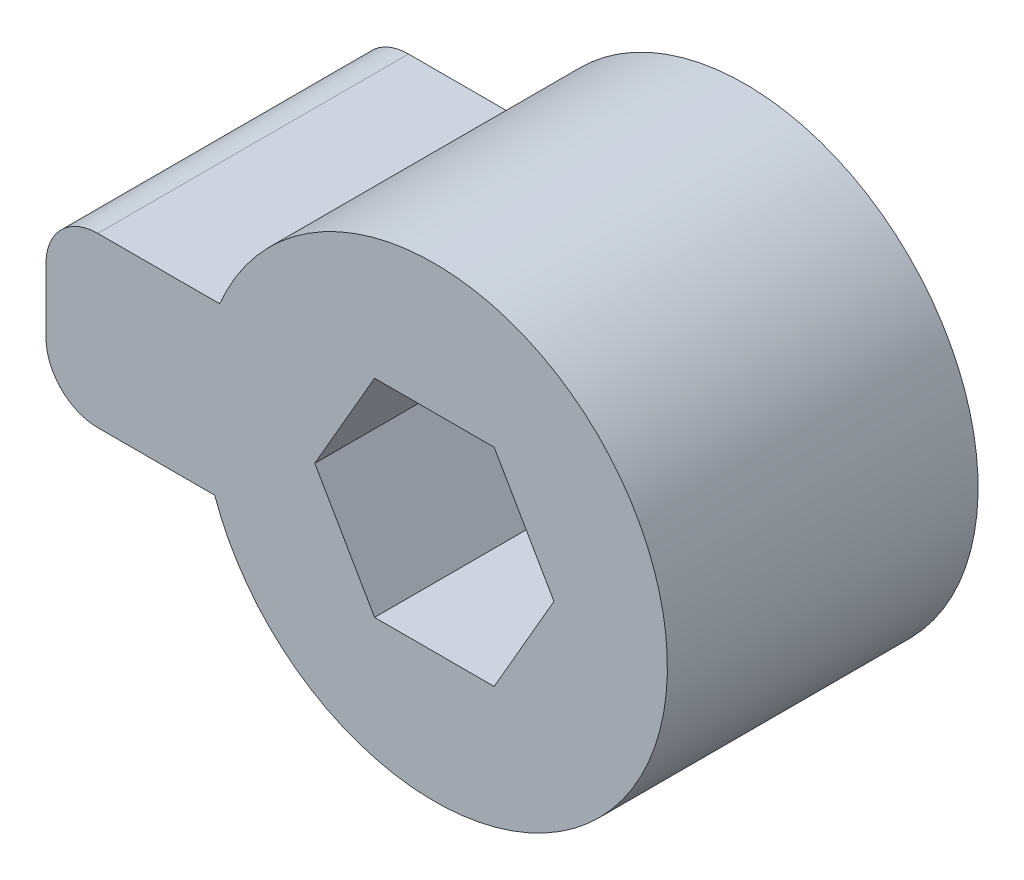
SolidWorks part; units mm, degrees
ref_plane "Front Plane" through (0, 0, 0) normal (0, 0, 1) x (1, 0, 0)
ref_plane "Top Plane" through (0, 0, 0) normal (0, 1, 0) x (1, 0, 0)
ref_plane "Right Plane" through (0, 0, 0) normal (1, 0, 0) x (0, 0, -1)
sketch "Sketch1" plane through (0, 0, 0) normal (0, 0, 1) x (1, 0, 0)
  line L0 (4.3947, 0) -> (6.7041, 0)
  line L1 (5.5494, 0) -> (5.5494, 2) construction
  line L3 (4.3947, 4) -> (3.24, 2)
  line L4 (6.7041, 4) -> (4.3947, 4)
  line L5 (7.8588, 2) -> (6.7041, 4)
  line L6 (6.7041, 0) -> (7.8588, 2)
  line L8 (3.24, 2) -> (4.3947, 0)
  line L9 (1.0426, 5.8059) -> (2.0853, 4) [skipped]
  circle A0 centre (5.5494, 2) radius 4.5
  point P17 (5.5494, 2)
  dimension "D2" = 4
  dimension "D5" = 9
  dimension "D1" = 6
  dimension "D3" = 4
  dimension "D4" = 4
extrude "Boss-Extrude1" add sketch "Sketch1" along normal blind 6
ref_plane "Plane1" through (0, 2, 0) normal (0, 1, 0) x (1, 0, 0)
sketch "Sketch2" plane through (0, 2, 0) normal (0, 1, 0) x (1, 0, 0)
  line L0 (3.24, 0) -> (1.0494, 0)
  line L2 (1.0494, -6) -> (3.24, -6)
  line L3 (1.0494, -6) -> (10.0494, -6) construction
  line L4 (3.24, -6) -> (3.24, 0)
  line L6 (1.0494, 0) -> (-1.9506, 0)
  line L7 (-1.9506, -6) -> (1.0494, -6)
  line L8 (-1.9506, 0) -> (-1.9506, -6)
  point P4 (-2.8646, 0)
  dimension "D1" = 3
extrude "Boss-Extrude2" add sketch "Sketch2" along normal blind 1.75 and the other way blind 1.5
fillet "Fillet1" radius 1 2 edges at (-1.9506, 3.75, 3) (-1.9506, 0.5, 3)
